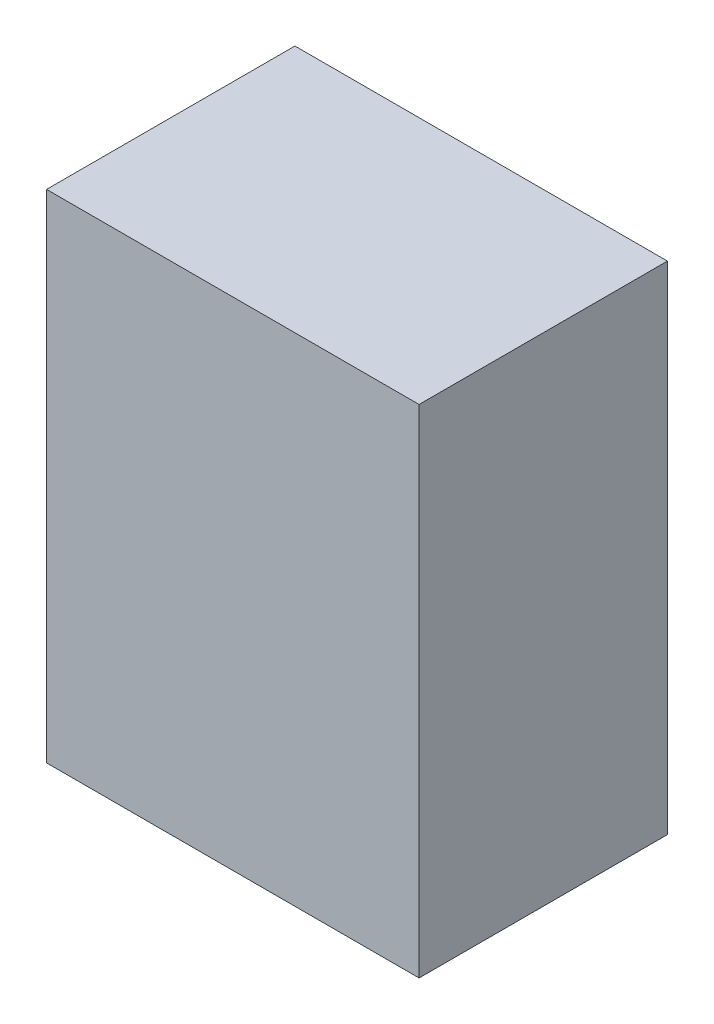
SolidWorks part; units mm, degrees
ref_plane "Front Plane" through (0, 0, 0) normal (0, 0, 1) x (1, 0, 0)
ref_plane "Top Plane" through (0, 0, 0) normal (0, 1, 0) x (1, 0, 0)
ref_plane "Right Plane" through (0, 0, 0) normal (1, 0, 0) x (0, 0, -1)
sketch "Sketch1" plane through (0, 0, 0) normal (0, 1, 0) x (1, 0, 0)
  line L1 (0, 0) -> (38.1, 0)
  line L2 (0, 0) -> (0, 25.4)
  line L3 (0, 25.4) -> (38.1, 25.4)
  line L4 (38.1, 0) -> (38.1, 25.4)
  dimension "D1" = 25.4
  dimension "D2" = 38.1
extrude "Boss-Extrude1" add sketch "Sketch1" along normal blind 50.8
